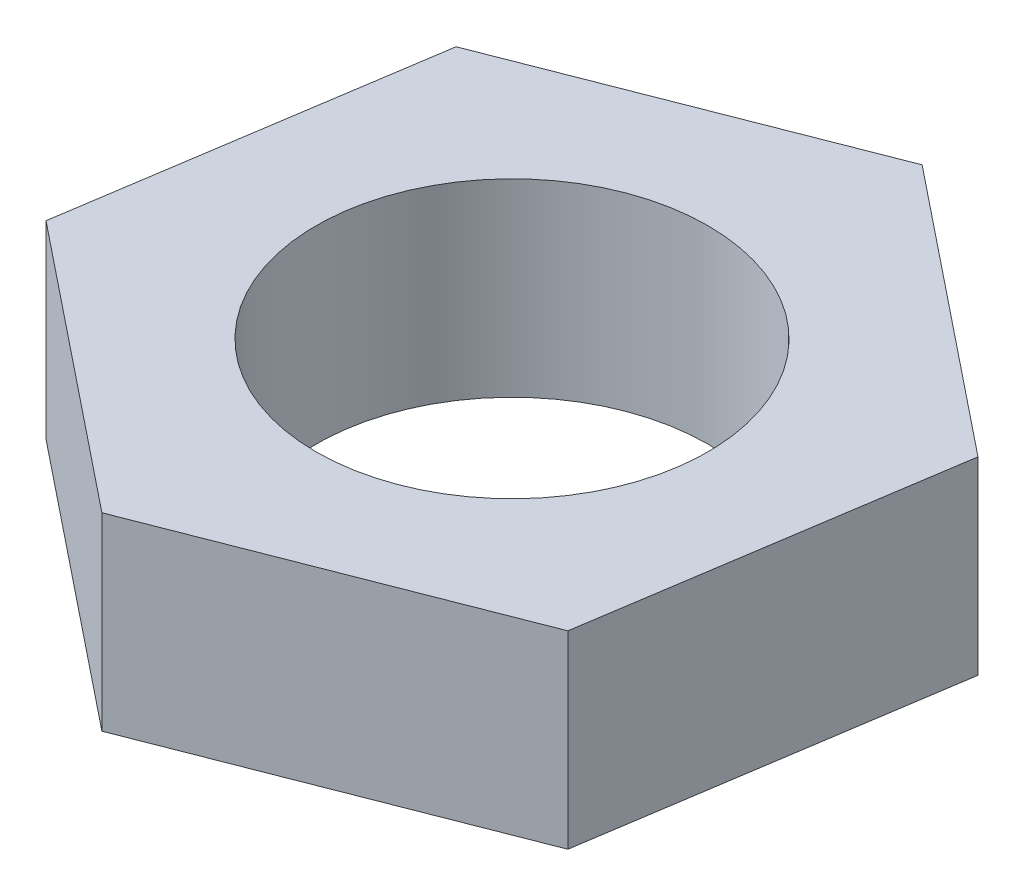
SolidWorks part; units mm, degrees
ref_plane "Plan de face" through (0, 0, 0) normal (0, 0, 1) x (1, 0, 0)
ref_plane "Plan de dessus" through (0, 0, 0) normal (0, 1, 0) x (1, 0, 0)
ref_plane "Plan de droite" through (0, 0, 0) normal (1, 0, 0) x (0, 0, -1)
sketch "Esquisse1" plane through (0, 0, 0) normal (0, 1, 0) x (1, 0, 0)
  line L1 (-12.405, -4.838) -> (-2.0127, -13.162)
  line L2 (-2.0127, -13.162) -> (10.3923, -8.3241)
  line L3 (10.3923, -8.3241) -> (12.405, 4.838)
  line L4 (12.405, 4.838) -> (2.0127, 13.162)
  line L5 (2.0127, 13.162) -> (-10.3923, 8.3241)
  line L6 (-10.3923, 8.3241) -> (-12.405, -4.838)
  circle A0 centre (0, 0) radius 11.5312 construction
  dimension "D1" = 18
extrude "Boss.-Extru.1" add sketch "Esquisse1" along normal blind 7
sketch "Esquisse2" plane through (0, 7, 0) normal (0, 1, 0) x (1, 0, 0)
  circle A0 centre (0, 0) radius 7.25
  dimension "D1" = 14.5
extrude "Enlèv. mat.-Extru.1" cut sketch "Esquisse2" against normal blind 7
cosmetic thread "Représentation de filetage1" parameters "D2"=16
cosmetic thread "Représentation de filetage2" parameters "D2"=16
